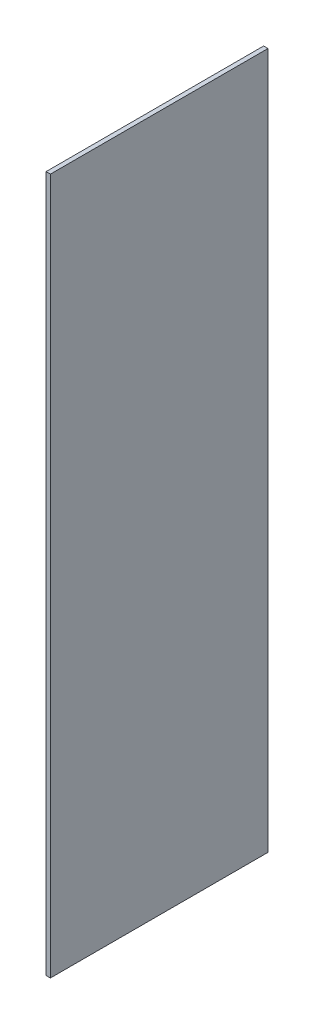
SolidWorks part; units mm, degrees
ref_plane "Front Plane" through (0, 0, 0) normal (0, 0, 1) x (1, 0, 0)
ref_plane "Top Plane" through (0, 0, 0) normal (0, 1, 0) x (1, 0, 0)
ref_plane "Right Plane" through (0, 0, 0) normal (1, 0, 0) x (0, 0, -1)
sketch "Sketch1" plane through (0, 0, 0) normal (0, 0, 1) x (1, 0, 0)
  line L1 (0, 0) -> (0.1, 0)
  line L2 (0, 0) -> (0, 16)
  line L3 (0, 16) -> (0.1, 16)
  line L4 (0.1, 0) -> (0.1, 16)
  dimension "D2" = 0.1
extrude "Boss-Extrude1" add sketch "Sketch1" along normal blind 5
equation "\"A.L\"= 0.07m"
equation "\"A.h\"= 0.007m"
equation "\"A.d\"= 0.005m"
equation "\"A.delta\"= 45.0001"
equation "\"A.w\"= 0m"
equation "\"A.v\"= 0.013m"
equation "\"A.s\"= 0.014m"
equation "\"A.t\"= 0.007m"
equation "\"B.L\"= 0.065m"
equation "\"B.h\"= 0.008m"
equation "\"B.s\"= 0.016m"
equation "\"B.t\"= 0.008m"
equation "\"C.h\"= 0.0065m"
equation "\"C.d\"= 0.005m"
equation "\"C.L\"= 0.05m"
equation "\"C.wmax\"= 0.003m"
equation "\"D.L\"= 0.06m"
equation "\"D.h\"= 0.008m"
equation "\"D.s\"= 0.012m"
equation "\"D.t\"= 0.008m"
equation "\"a_h\"= 0.0001m"
equation "\"a_d\"= 0.005m"
equation "\"a_L\"= 0.008m"
equation "\"b_h\"= 0.0004m"
equation "\"b_d\"= 0.005m"
equation "\"b_L\"= 0.007m"
equation "\"c_h\"= 0.0001m"
equation "\"c_d\"= 0.005m"
equation "\"c_L\"= 0.01m"
equation "\"d_h\"= 0.0001m"
equation "\"d_d\"= 0.005m"
equation "\"d_L\"= 0.01m"
equation "\"S.h\"= 0.015m"
equation "\"S.L\"= 0.09275m"
equation "\"D1@Sketch1\"=\"c_L\"+0.006"
equation "\"D2@Sketch1\"=\"c_h\""
equation "\"D1@Boss-Extrude1\"=0.005m"
